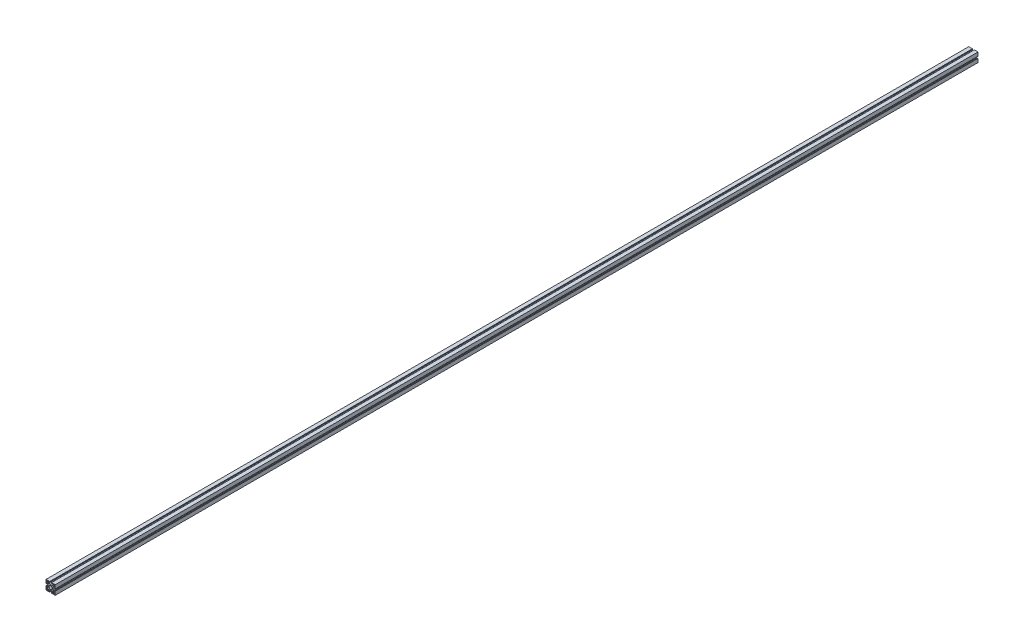
SolidWorks part; units mm, degrees
ref_plane "Alzado" through (0, 0, 0) normal (0, 0, 1) x (1, 0, 0)
ref_plane "Planta" through (0, 0, 0) normal (0, 1, 0) x (1, 0, 0)
ref_plane "Vista lateral" through (0, 0, 0) normal (1, 0, 0) x (0, 0, -1)
sketch "Croquis1" plane through (0, 0, 0) normal (0, 0, 1) x (1, 0, 0)
  line L1 (-20, -20) -> (-4.095, -20)
  line L2 (-20, -20) -> (-20, -4.095)
  line L3 (-20, 20) -> (-4.095, 20)
  line L4 (20, -20) -> (20, -4.095)
  line L5 (-20, -20) -> (20, 20) construction
  line L6 (-20, 20) -> (20, -20) construction
  line L11 (-15.5, 15.5) -> (15.5, -15.5) construction
  line L12 (-15.5, -15.5) -> (15.5, 15.5) construction
  line L13 (-19.49, -4.095) -> (-20, -4.095)
  line L18 (-10.0038, 10) -> (10.0038, -10) construction
  line L19 (-10.0038, -10) -> (10.0038, 10) construction
  line L24 (-11, 11) -> (11, -11) construction
  line L25 (-11, -11) -> (11, 11) construction
  line L26 (-19.19, -4.7304) -> (-19.19, -4.395)
  line L27 (-14.109, -13.4227) -> (-13.7376, -13.0513)
  line L28 (-13.7376, -13.0513) -> (-13.0513, -13.7376)
  line L29 (-15.1464, -15.1464) -> (-15.1649, -15.1487)
  line L30 (-16.891, -13.4227) -> (-17.2624, -13.0513)
  line L31 (-17.5773, -14.109) -> (-17.9487, -13.7376)
  line L32 (-17.9487, -13.7376) -> (-17.2624, -13.0513)
  line L33 (-13.4227, -14.109) -> (-13.0513, -13.7376)
  line L34 (-13.4227, -16.891) -> (-13.0513, -17.2624)
  line L35 (-13.0513, -17.2624) -> (-13.7376, -17.9487)
  line L36 (-14.109, -17.5773) -> (-13.7376, -17.9487)
  line L37 (-16.891, -17.5773) -> (-17.2624, -17.9487)
  line L38 (-17.2624, -17.9487) -> (-17.9487, -17.2624)
  line L39 (-17.5773, -16.891) -> (-17.9487, -17.2624)
  line L40 (-14.109, 13.4227) -> (-13.7376, 13.0513)
  line L41 (-20, 20) -> (-4.095, 20)
  line L43 (-20, -20) -> (-4.095, -20)
  line L44 (20, 20) -> (20, 4.095)
  line L45 (-13.4227, 14.109) -> (-13.0513, 13.7376)
  line L46 (-13.0513, 13.7376) -> (-13.7376, 13.0513)
  line L47 (-13.4227, 16.891) -> (-13.0513, 17.2624)
  line L48 (-14.109, 17.5773) -> (-13.7376, 17.9487)
  line L49 (-13.7376, 17.9487) -> (-13.0513, 17.2624)
  line L50 (-17.2624, 13.0513) -> (-17.9487, 13.7376)
  line L51 (-16.891, 13.4227) -> (-17.2624, 13.0513)
  line L52 (-17.5773, 14.109) -> (-17.9487, 13.7376)
  line L53 (-17.5773, 16.891) -> (-17.9487, 17.2624)
  line L54 (-17.9487, 17.2624) -> (-17.2624, 17.9487)
  line L55 (-16.891, 17.5773) -> (-17.2624, 17.9487)
  line L56 (13.4227, 14.109) -> (13.0513, 13.7376)
  line L57 (20, 20) -> (20, 4.095)
  line L58 (20, 20) -> (4.095, 20)
  line L59 (-20, 20) -> (-20, 4.095)
  line L60 (20, -20) -> (4.095, -20)
  line L61 (14.109, 13.4227) -> (13.7376, 13.0513)
  line L62 (13.7376, 13.0513) -> (13.0513, 13.7376)
  line L63 (16.891, 13.4227) -> (17.2624, 13.0513)
  line L64 (17.5773, 14.109) -> (17.9487, 13.7376)
  line L65 (17.9487, 13.7376) -> (17.2624, 13.0513)
  line L66 (13.0513, 17.2624) -> (13.7376, 17.9487)
  line L67 (13.4227, 16.891) -> (13.0513, 17.2624)
  line L68 (14.109, 17.5773) -> (13.7376, 17.9487)
  line L69 (16.891, 17.5773) -> (17.2624, 17.9487)
  line L70 (17.2624, 17.9487) -> (17.9487, 17.2624)
  line L71 (17.5773, 16.891) -> (17.9487, 17.2624)
  line L72 (14.109, -13.4227) -> (13.7376, -13.0513)
  line L73 (20, -20) -> (4.095, -20)
  line L74 (20, -20) -> (20, -4.095)
  line L75 (20, 20) -> (4.095, 20)
  line L76 (-20, -20) -> (-20, -4.095)
  line L77 (13.4227, -14.109) -> (13.0513, -13.7376)
  line L78 (13.0513, -13.7376) -> (13.7376, -13.0513)
  line L79 (13.4227, -16.891) -> (13.0513, -17.2624)
  line L80 (14.109, -17.5773) -> (13.7376, -17.9487)
  line L81 (13.7376, -17.9487) -> (13.0513, -17.2624)
  line L82 (17.2624, -13.0513) -> (17.9487, -13.7376)
  line L83 (16.891, -13.4227) -> (17.2624, -13.0513)
  line L84 (17.5773, -14.109) -> (17.9487, -13.7376)
  line L85 (17.5773, -16.891) -> (17.9487, -17.2624)
  line L86 (17.9487, -17.2624) -> (17.2624, -17.9487)
  line L87 (16.891, -17.5773) -> (17.2624, -17.9487)
  line L88 (-11, -15) -> (-11, -17.69)
  line L89 (11, -15) -> (11, -17.69)
  line L90 (-7, -11) -> (7, -11)
  line L91 (-10.5, -18.19) -> (-6.7064, -18.19)
  line L92 (-6.7064, -18.19) -> (-6.7064, -16.69)
  line L93 (-6.2064, -16.19) -> (-4.395, -16.19)
  line L94 (-4.095, -16.49) -> (-4.095, -17.89)
  line L95 (-4.395, -18.19) -> (-4.7304, -18.19)
  line L96 (-4.7304, -18.19) -> (-4.7304, -19.19)
  line L97 (-4.7304, -19.19) -> (-4.395, -19.19)
  line L98 (-4.095, -19.49) -> (-4.095, -20)
  line L99 (-4.095, -20) -> (-11, -20)
  line L100 (10.5, -18.19) -> (6.7064, -18.19)
  line L101 (6.7064, -18.19) -> (6.7064, -16.69)
  line L102 (6.2064, -16.19) -> (4.395, -16.19)
  line L103 (4.095, -16.49) -> (4.095, -17.89)
  line L104 (4.395, -18.19) -> (4.7304, -18.19)
  line L105 (4.7304, -18.19) -> (4.7304, -19.19)
  line L106 (4.7304, -19.19) -> (4.395, -19.19)
  line L107 (4.095, -19.49) -> (4.095, -20)
  line L108 (4.095, -20) -> (20, -20)
  line L109 (-4.095, -20) -> (-20, -20)
  line L110 (4.095, -20) -> (20, -20)
  line L111 (-4.095, -20) -> (-20, -20)
  line L112 (-18.19, -4.7304) -> (-19.19, -4.7304)
  line L113 (-18.19, -4.395) -> (-18.19, -4.7304)
  line L114 (-16.49, -4.095) -> (-17.89, -4.095)
  line L115 (-16.19, -6.2064) -> (-16.19, -4.395)
  line L116 (-18.19, -6.7064) -> (-16.69, -6.7064)
  line L117 (-18.19, -10.5) -> (-18.19, -6.7064)
  line L118 (-15, -11) -> (-17.69, -11)
  line L119 (-11, 7) -> (-11, -7)
  line L120 (-15, 11) -> (-17.69, 11)
  line L121 (-18.19, 10.5) -> (-18.19, 6.7064)
  line L122 (-18.19, 6.7064) -> (-16.69, 6.7064)
  line L123 (-16.19, 6.2064) -> (-16.19, 4.395)
  line L124 (-16.49, 4.095) -> (-17.89, 4.095)
  line L125 (-18.19, 4.395) -> (-18.19, 4.7304)
  line L126 (-18.19, 4.7304) -> (-19.19, 4.7304)
  line L127 (-19.19, 4.7304) -> (-19.19, 4.395)
  line L128 (-19.49, 4.095) -> (-20, 4.095)
  line L129 (-4.095, 19.49) -> (-4.095, 20)
  line L130 (-4.7304, 19.19) -> (-4.395, 19.19)
  line L131 (-4.7304, 18.19) -> (-4.7304, 19.19)
  line L132 (-4.395, 18.19) -> (-4.7304, 18.19)
  line L133 (-4.095, 16.49) -> (-4.095, 17.89)
  line L134 (-6.2064, 16.19) -> (-4.395, 16.19)
  line L135 (-6.7064, 18.19) -> (-6.7064, 16.69)
  line L136 (-10.5, 18.19) -> (-6.7064, 18.19)
  line L137 (-11, 15) -> (-11, 17.69)
  line L138 (7, 11) -> (-7, 11)
  line L139 (11, 15) -> (11, 17.69)
  line L140 (10.5, 18.19) -> (6.7064, 18.19)
  line L141 (6.7064, 18.19) -> (6.7064, 16.69)
  line L142 (6.2064, 16.19) -> (4.395, 16.19)
  line L143 (4.095, 16.49) -> (4.095, 17.89)
  line L144 (4.395, 18.19) -> (4.7304, 18.19)
  line L145 (4.7304, 18.19) -> (4.7304, 19.19)
  line L146 (4.7304, 19.19) -> (4.395, 19.19)
  line L147 (4.095, 19.49) -> (4.095, 20)
  line L148 (19.49, 4.095) -> (20, 4.095)
  line L149 (19.19, 4.7304) -> (19.19, 4.395)
  line L150 (18.19, 4.7304) -> (19.19, 4.7304)
  line L151 (18.19, 4.395) -> (18.19, 4.7304)
  line L152 (16.49, 4.095) -> (17.89, 4.095)
  line L153 (16.19, 6.2064) -> (16.19, 4.395)
  line L154 (18.19, 6.7064) -> (16.69, 6.7064)
  line L155 (18.19, 10.5) -> (18.19, 6.7064)
  line L156 (15, 11) -> (17.69, 11)
  line L157 (11, -7) -> (11, 7)
  line L158 (15, -11) -> (17.69, -11)
  line L159 (18.19, -10.5) -> (18.19, -6.7064)
  line L160 (18.19, -6.7064) -> (16.69, -6.7064)
  line L161 (16.19, -6.2064) -> (16.19, -4.395)
  line L162 (16.49, -4.095) -> (17.89, -4.095)
  line L163 (18.19, -4.395) -> (18.19, -4.7304)
  line L164 (18.19, -4.7304) -> (19.19, -4.7304)
  line L165 (19.19, -4.7304) -> (19.19, -4.395)
  line L166 (19.49, -4.095) -> (20, -4.095)
  line L167 (20, 4.095) -> (20, 20)
  line L168 (20, 4.095) -> (20, 20)
  line L169 (20, -4.095) -> (20, -20)
  line L170 (20, -4.095) -> (20, -20)
  line L171 (-20, 4.095) -> (-20, 20)
  line L172 (-20, -4.095) -> (-20, -20)
  line L173 (-20, -4.095) -> (-20, -20)
  line L174 (-20, 4.095) -> (-20, 20)
  line L175 (4.095, 20) -> (20, 20)
  line L176 (4.095, 20) -> (20, 20)
  line L177 (-4.095, 20) -> (-20, 20)
  line L178 (-4.095, 20) -> (-20, 20)
  line L179 (-20, 20) -> (-20, 4.095) [skipped]
  line L180 (-20, 4.095) -> (-20, 20)
  circle A0 centre (0, 0) radius 6.85
  arc A3 (-17.5773, -14.109) -> (-17.5773, -16.891) centre (-15.5, -15.5) ccw
  arc A5 (-14.109, -13.4227) -> (-16.891, -13.4227) centre (-15.5, -15.5) ccw
  arc A6 (-13.4227, -16.891) -> (-13.4227, -14.109) centre (-15.5, -15.5) ccw
  arc A7 (-16.891, -17.5773) -> (-14.109, -17.5773) centre (-15.5, -15.5) ccw
  arc A8 (-13.4227, 14.109) -> (-13.4227, 16.891) centre (-15.5, 15.5) ccw
  arc A9 (-14.109, 17.5773) -> (-16.891, 17.5773) centre (-15.5, 15.5) ccw
  arc A10 (-17.5773, 16.891) -> (-17.5773, 14.109) centre (-15.5, 15.5) ccw
  arc A11 (-16.891, 13.4227) -> (-14.109, 13.4227) centre (-15.5, 15.5) ccw
  arc A12 (14.109, 13.4227) -> (16.891, 13.4227) centre (15.5, 15.5) ccw
  arc A13 (17.5773, 14.109) -> (17.5773, 16.891) centre (15.5, 15.5) ccw
  arc A14 (16.891, 17.5773) -> (14.109, 17.5773) centre (15.5, 15.5) ccw
  arc A15 (13.4227, 16.891) -> (13.4227, 14.109) centre (15.5, 15.5) ccw
  arc A16 (13.4227, -14.109) -> (13.4227, -16.891) centre (15.5, -15.5) ccw
  arc A17 (14.109, -17.5773) -> (16.891, -17.5773) centre (15.5, -15.5) ccw
  arc A18 (17.5773, -16.891) -> (17.5773, -14.109) centre (15.5, -15.5) ccw
  arc A19 (16.891, -13.4227) -> (14.109, -13.4227) centre (15.5, -15.5) ccw
  arc A20 (7, -11) -> (11, -15) centre (7, -15) cw
  arc A21 (-7, -11) -> (-11, -15) centre (-7, -15) ccw
  arc A22 (-4.395, -16.19) -> (-4.095, -16.49) centre (-4.395, -16.49) cw
  arc A23 (-4.095, -17.89) -> (-4.395, -18.19) centre (-4.395, -17.89) cw
  arc A24 (-6.2064, -16.19) -> (-6.7064, -16.69) centre (-6.2064, -16.69) ccw
  arc A25 (-4.095, -19.49) -> (-4.395, -19.19) centre (-4.395, -19.49) ccw
  arc A26 (-11, -17.69) -> (-10.5, -18.19) centre (-10.5, -17.69) ccw
  arc A27 (11, -17.69) -> (10.5, -18.19) centre (10.5, -17.69) cw
  arc A28 (6.2064, -16.19) -> (6.7064, -16.69) centre (6.2064, -16.69) cw
  arc A29 (4.395, -16.19) -> (4.095, -16.49) centre (4.395, -16.49) ccw
  arc A30 (4.095, -17.89) -> (4.395, -18.19) centre (4.395, -17.89) ccw
  arc A31 (4.095, -19.49) -> (4.395, -19.19) centre (4.395, -19.49) cw
  arc A32 (-19.49, -4.095) -> (-19.19, -4.395) centre (-19.49, -4.395) cw
  arc A33 (-17.89, -4.095) -> (-18.19, -4.395) centre (-17.89, -4.395) ccw
  arc A34 (-16.19, -4.395) -> (-16.49, -4.095) centre (-16.49, -4.395) ccw
  arc A35 (-16.19, -6.2064) -> (-16.69, -6.7064) centre (-16.69, -6.2064) cw
  arc A36 (-17.69, -11) -> (-18.19, -10.5) centre (-17.69, -10.5) cw
  arc A37 (-11, -7) -> (-15, -11) centre (-15, -7) cw
  arc A38 (-11, 7) -> (-15, 11) centre (-15, 7) ccw
  arc A39 (-17.69, 11) -> (-18.19, 10.5) centre (-17.69, 10.5) ccw
  arc A40 (-16.19, 6.2064) -> (-16.69, 6.7064) centre (-16.69, 6.2064) ccw
  arc A41 (-16.19, 4.395) -> (-16.49, 4.095) centre (-16.49, 4.395) cw
  arc A42 (-17.89, 4.095) -> (-18.19, 4.395) centre (-17.89, 4.395) cw
  arc A43 (-19.49, 4.095) -> (-19.19, 4.395) centre (-19.49, 4.395) ccw
  arc A44 (-4.095, 19.49) -> (-4.395, 19.19) centre (-4.395, 19.49) cw
  arc A45 (-4.095, 17.89) -> (-4.395, 18.19) centre (-4.395, 17.89) ccw
  arc A46 (-4.395, 16.19) -> (-4.095, 16.49) centre (-4.395, 16.49) ccw
  arc A47 (-6.2064, 16.19) -> (-6.7064, 16.69) centre (-6.2064, 16.69) cw
  arc A48 (-11, 17.69) -> (-10.5, 18.19) centre (-10.5, 17.69) cw
  arc A49 (-7, 11) -> (-11, 15) centre (-7, 15) cw
  arc A50 (7, 11) -> (11, 15) centre (7, 15) ccw
  arc A51 (11, 17.69) -> (10.5, 18.19) centre (10.5, 17.69) ccw
  arc A52 (6.2064, 16.19) -> (6.7064, 16.69) centre (6.2064, 16.69) ccw
  arc A53 (4.395, 16.19) -> (4.095, 16.49) centre (4.395, 16.49) cw
  arc A54 (4.095, 17.89) -> (4.395, 18.19) centre (4.395, 17.89) cw
  arc A55 (4.095, 19.49) -> (4.395, 19.19) centre (4.395, 19.49) ccw
  arc A56 (19.49, 4.095) -> (19.19, 4.395) centre (19.49, 4.395) cw
  arc A57 (17.89, 4.095) -> (18.19, 4.395) centre (17.89, 4.395) ccw
  arc A58 (16.19, 4.395) -> (16.49, 4.095) centre (16.49, 4.395) ccw
  arc A59 (16.19, 6.2064) -> (16.69, 6.7064) centre (16.69, 6.2064) cw
  arc A60 (17.69, 11) -> (18.19, 10.5) centre (17.69, 10.5) cw
  arc A61 (11, 7) -> (15, 11) centre (15, 7) cw
  arc A62 (11, -7) -> (15, -11) centre (15, -7) ccw
  arc A63 (17.69, -11) -> (18.19, -10.5) centre (17.69, -10.5) ccw
  arc A64 (16.19, -6.2064) -> (16.69, -6.7064) centre (16.69, -6.2064) ccw
  arc A65 (16.19, -4.395) -> (16.49, -4.095) centre (16.49, -4.395) cw
  arc A66 (17.89, -4.095) -> (18.19, -4.395) centre (17.89, -4.395) cw
  arc A67 (19.49, -4.095) -> (19.19, -4.395) centre (19.49, -4.395) ccw
  point P0 (0, 0)
  point P47 (-15.5, -15.5)
  point P107 (0, 0)
  point P131 (-6.7064, -16.19)
  point P152 (0, 0)
  point P197 (0, 0)
  point P242 (0, 0)
  point P287 (0, 0)
  dimension "D3" = 13.7
  dimension "D6" = 4
  dimension "D7" = 4
  dimension "D9" = 5
  dimension "D12" = 0.3
  dimension "D13" = 0.5
  dimension "D14" = 0.5
  dimension "D2" = 40
  dimension "D4" = 4
  dimension "D5" = 31
  dimension "D10" = 4
  dimension "D11" = 2
extrude "Saliente-Extruir1" add sketch "Croquis1" along normal blind 4000 contours A31 L107 L60 L4 L3 L2 L1 L43 L98 A25 L97 L96 L95 A23 L94 A22 L93 A24 L92 L91 A26 L88 A21 L90 A20 L89 A27 L100 L101 A28 L102 A29 L103 A30 L104 L105 L106 A19 L83 L82 L84 A18 L85 L86 L87 A17 L80 L81 L79 A16
